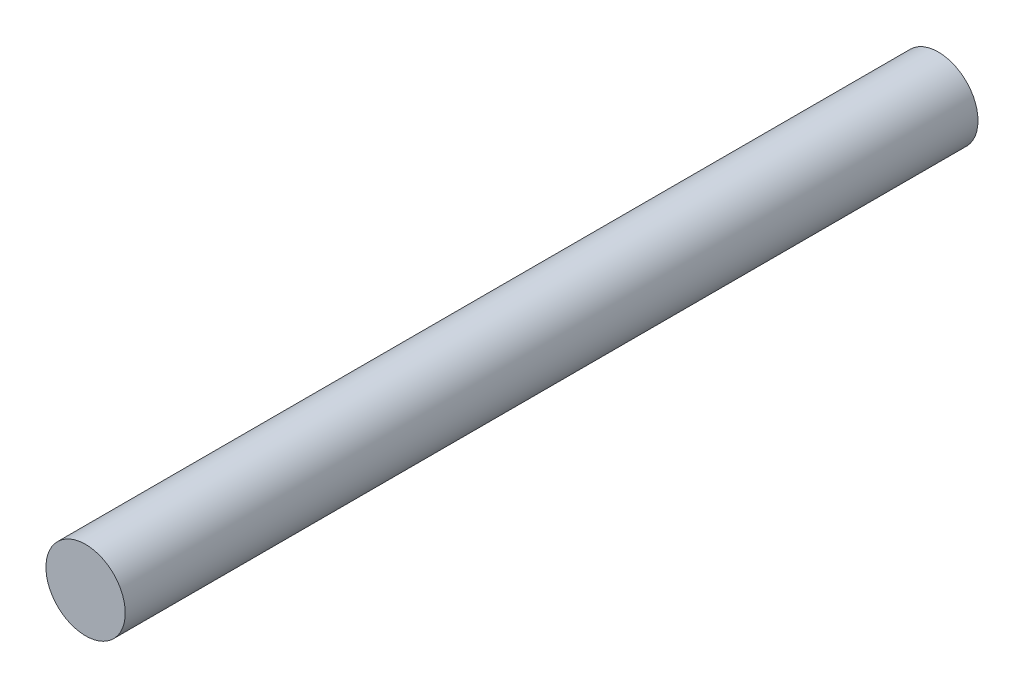
SolidWorks part; units mm, degrees
ref_plane "Front Plane" through (0, 0, 0) normal (0, 0, 1) x (1, 0, 0)
ref_plane "Top Plane" through (0, 0, 0) normal (0, 1, 0) x (1, 0, 0)
ref_plane "Right Plane" through (0, 0, 0) normal (1, 0, 0) x (0, 0, -1)
sketch "Sketch1" plane through (0, 0, 0) normal (0, 0, 1) x (1, 0, 0)
  circle A1 centre (0, 0) radius 2
  dimension "D1" = 4
extrude "Boss-Extrude1" add sketch "Sketch1" against normal blind 43
